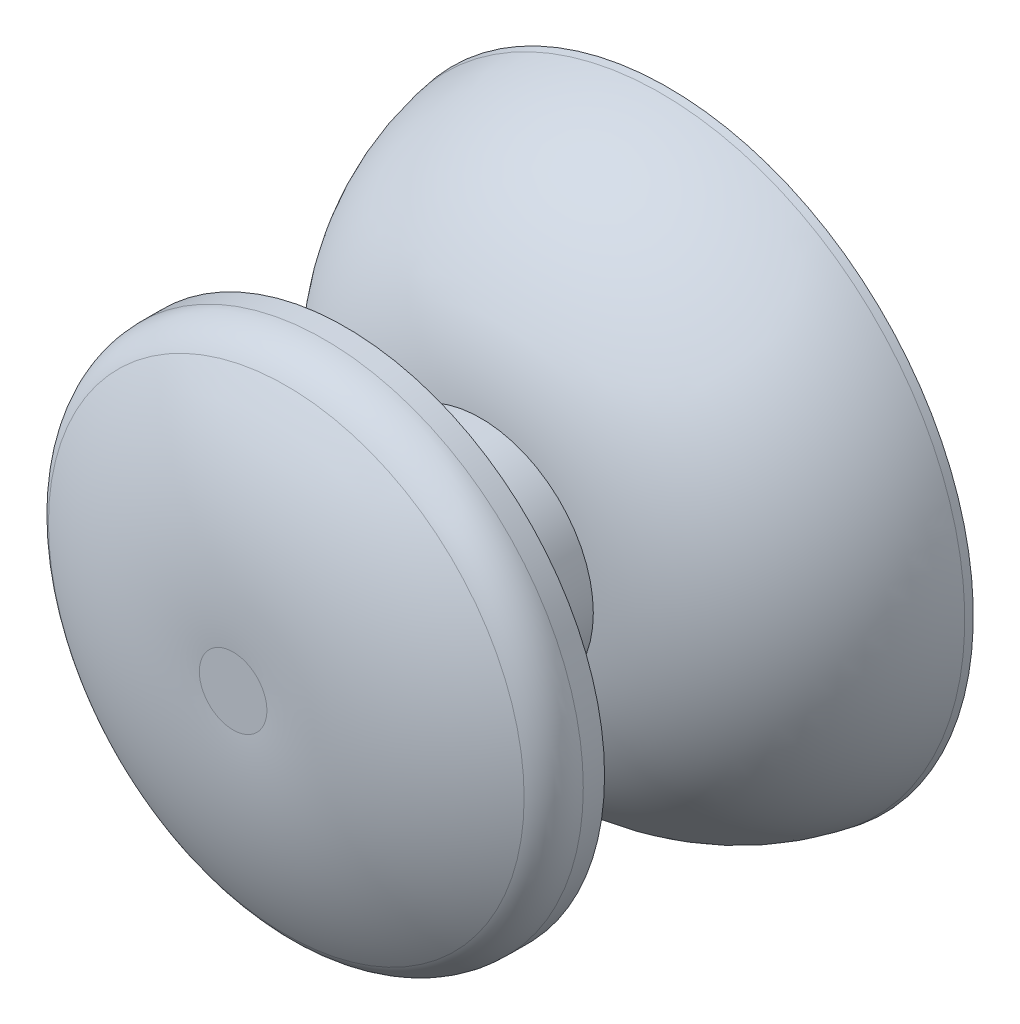
SolidWorks part; units mm, degrees
ref_plane "정면" through (0, 0, 0) normal (0, 0, 1) x (1, 0, 0)
ref_plane "윗면" through (0, 0, 0) normal (0, 1, 0) x (1, 0, 0)
ref_plane "우측면" through (0, 0, 0) normal (1, 0, 0) x (0, 0, -1)
ref_plane "평면1" through (0, 12.3611, 0) normal (0, -1, 0) x (1, 0, 0)
sketch "스케치1" plane through (0, 12.3611, 0) normal (0, -1, 0) x (1, 0, 0)
  line L0 (56.7886, 33.75) -> (55.2886, 33.75)
  line L1 (55.2886, 33.75) -> (55.2886, 24.5842)
  line L2 (55.2886, 24.5842) -> (56.9024, 24.5842)
  line L3 (56.9024, 24.5842) -> (56.9024, 19.6671)
  line L4 (56.9024, 19.6671) -> (64.1107, 19.6671)
  line L5 (67.2602, 14.75) -> (67.3296, 14.4243)
  line L6 (67.3296, 14.4243) -> (68.8424, 14.4243)
  line L7 (68.8424, 14.4243) -> (68.7886, 14.75)
  line L8 (60.2886, 22.75) -> (60.2886, 28.75)
  line L9 (60.2886, 28.75) -> (66.7886, 28.75)
  line L10 (66.7886, 28.75) -> (66.7886, 29.695)
  line L11 (55.2886, 33.7708) -> (55.2886, 14.4243) construction
  arc A0 (64.1107, 19.6671) -> (67.2602, 14.75) centre (59.1451, 13.0194) cw
  arc A1 (68.7886, 14.75) -> (60.2886, 22.75) centre (59.1451, 13.0194) ccw
  arc A2 (66.7886, 29.695) -> (65.8536, 31.3879) centre (64.7886, 29.695) ccw
  arc A3 (65.8536, 31.3879) -> (56.7886, 33.75) centre (57.5913, 18.2553) ccw
revolve "회전1" add sketch "스케치1" angle 360 about L11
